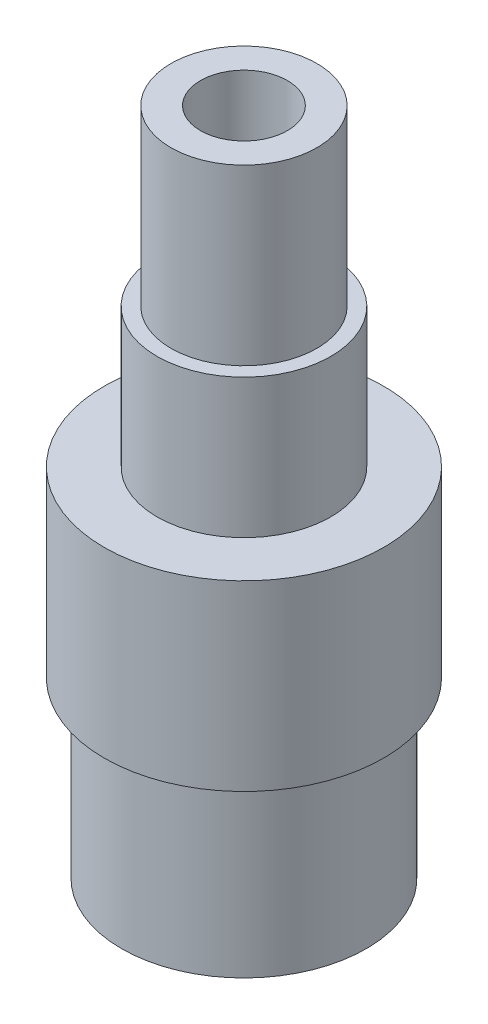
SolidWorks part; units mm, degrees
ref_plane "Front Plane" through (0, 0, 0) normal (0, 0, 1) x (1, 0, 0)
ref_plane "Top Plane" through (0, 0, 0) normal (0, 1, 0) x (1, 0, 0)
ref_plane "Right Plane" through (0, 0, 0) normal (1, 0, 0) x (0, 0, -1)
sketch "Sketch1" plane through (0, 0, 0) normal (0, 0, 1) x (1, 0, 0)
  line L0 (-3.175, 0) -> (-5.334, 0)
  line L1 (-6.35, -12.7) -> (-6.35, -22.86)
  line L2 (-6.35, -22.86) -> (-10.2108, -22.86)
  line L3 (-10.2108, -22.86) -> (-10.2108, -36.195)
  line L4 (-10.2108, -36.195) -> (-8.9408, -36.195)
  line L5 (-8.9408, -36.195) -> (-8.9408, -48.895)
  line L6 (-8.9408, -48.895) -> (-4.445, -48.895)
  line L7 (-4.445, -48.895) -> (-4.445, -43.18)
  line L8 (-4.445, -43.18) -> (-3.175, -43.18)
  line L9 (-3.175, -43.18) -> (-3.175, 0)
  line L10 (0, 0) -> (0, -16.6803) construction
  line L11 (-5.334, 0) -> (-5.334, -12.7)
  line L12 (-5.334, -12.7) -> (-6.35, -12.7)
  dimension "D1" = 5.715
  dimension "D2" = 3.175
  dimension "D3" = 10.2108
  dimension "D4" = 6.35
  dimension "D5" = 1.27
  dimension "D6" = 1.27
  dimension "D7" = 10.16
  dimension "D8" = 13.335
  dimension "D9" = 12.7
  dimension "D10" = 4.445
  dimension "D11" = 12.7
  dimension "D12" = 5.334
  dimension "D13" = 8.9408
revolve "Revolve1" add sketch "Sketch1" angle 360 about L10
